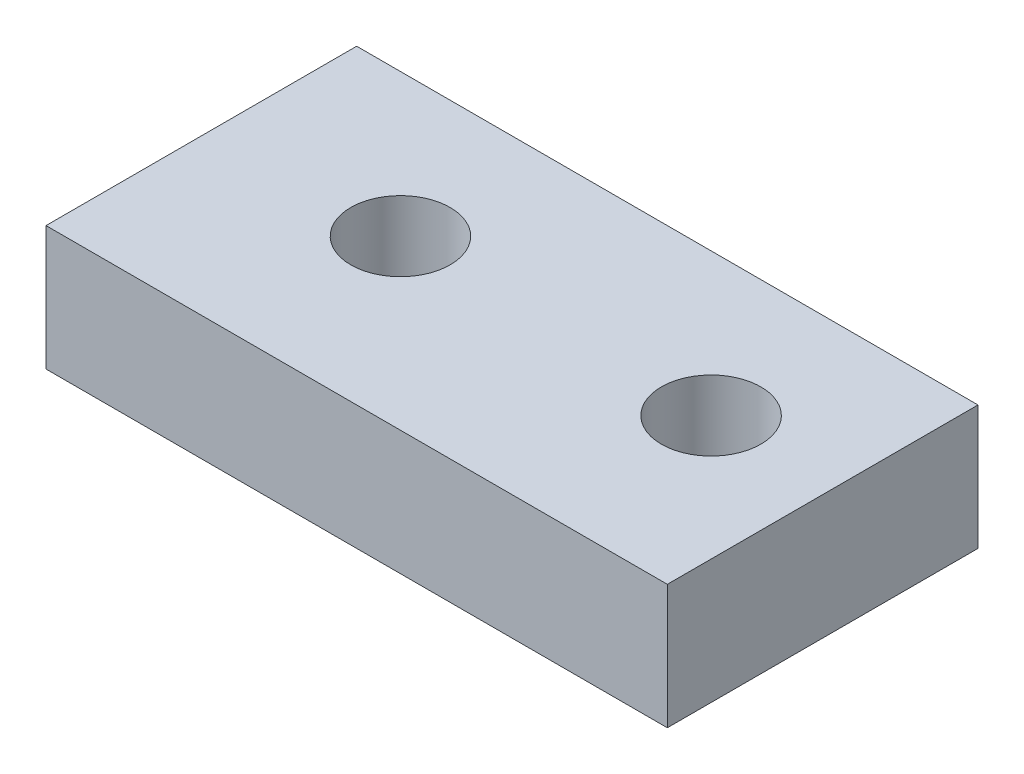
SolidWorks part; units mm, degrees
ref_plane "Front Plane" through (0, 0, 0) normal (0, 0, 1) x (1, 0, 0)
ref_plane "Top Plane" through (0, 0, 0) normal (0, 1, 0) x (1, 0, 0)
ref_plane "Right Plane" through (0, 0, 0) normal (1, 0, 0) x (0, 0, -1)
sketch "Sketch1" plane through (0, 0, 0) normal (0, 1, 0) x (1, 0, 0)
  line L1 (-3.7696, 2.2954) -> (6.2304, 2.2954)
  line L2 (-3.7696, 2.2954) -> (-3.7696, -2.7046)
  line L3 (-3.7696, -2.7046) -> (6.2304, -2.7046)
  line L4 (6.2304, 2.2954) -> (6.2304, -2.7046)
  circle A0 centre (-0.7696, 0) radius 0.8
  circle A1 centre (4.2304, 0) radius 0.8
  dimension "D3" = 5
  dimension "D4" = 2
  dimension "D1" = 10
  dimension "D2" = 5
extrude "Boss-Extrude1" add sketch "Sketch1" along normal blind 2
